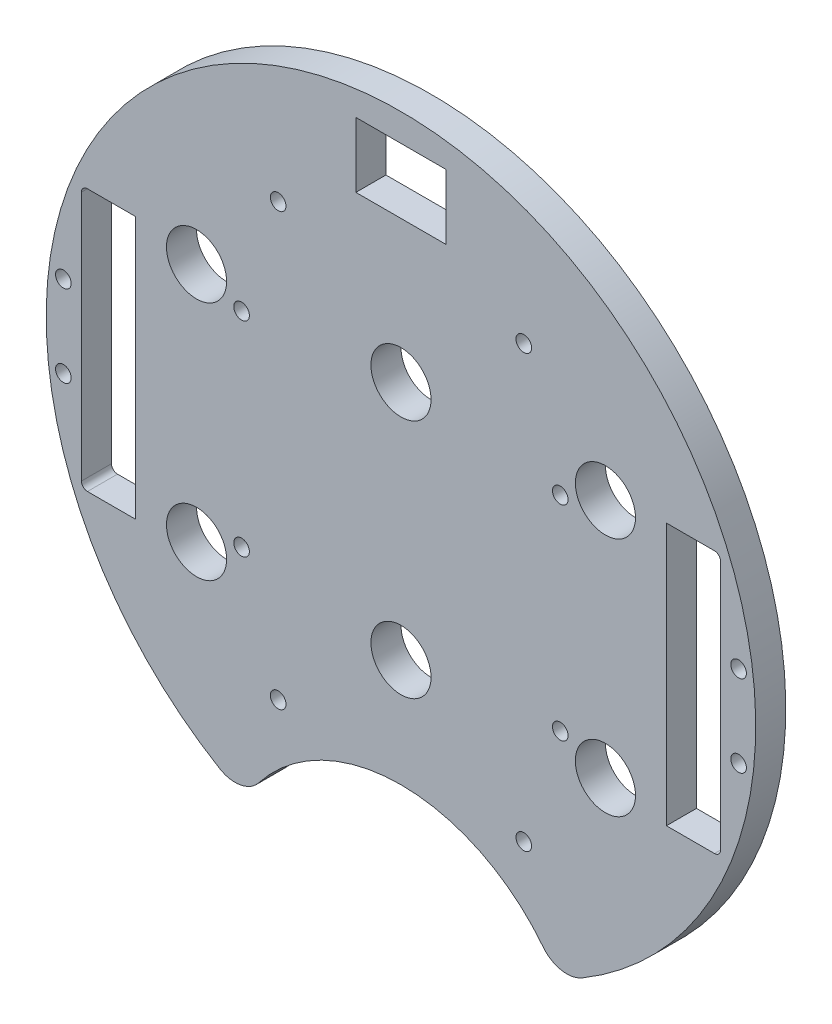
SolidWorks part; units mm, degrees
ref_plane "Front Plane" through (0, 0, 0) normal (0, 0, 1) x (1, 0, 0)
ref_plane "Top Plane" through (0, 0, 0) normal (0, 1, 0) x (1, 0, 0)
ref_plane "Right Plane" through (0, 0, 0) normal (1, 0, 0) x (0, 0, -1)
sketch "Sketch1" plane through (0, 0, 0) normal (0, 0, 1) x (1, 0, 0)
  line L0 (0, 0) -> (-82.1241, 0) construction
  line L1 (0, 0) -> (0, 95.6219) construction
  line L2 (67.494, 26.416) -> (67.494, -26.416)
  line L3 (-66.224, 27.686) -> (-56.064, 27.686)
  line L4 (-67.494, 26.416) -> (-67.494, -26.416)
  line L5 (-66.224, -27.686) -> (-56.064, -27.686)
  line L6 (-56.064, 27.686) -> (-56.064, -27.686)
  line L7 (66.224, -27.686) -> (56.064, -27.686)
  line L8 (66.224, 27.686) -> (56.064, 27.686)
  line L9 (56.064, 27.686) -> (56.064, -27.686)
  arc A0 (-69.526, -27.94) -> (69.526, -27.94) centre (0, 0) ccw
  arc A9 (69.526, 27.94) -> (-69.526, 27.94) centre (0, 0) ccw
  circle A10 centre (0, 0) radius 74.93
  arc A11 (66.224, 27.686) -> (67.494, 26.416) centre (66.224, 26.416) cw
  arc A12 (66.224, -27.686) -> (67.494, -26.416) centre (66.224, -26.416) ccw
  arc A13 (-66.224, 27.686) -> (-67.494, 26.416) centre (-66.224, 26.416) ccw
  arc A14 (-66.224, -27.686) -> (-67.494, -26.416) centre (-66.224, -26.416) cw
  dimension "D13" = 1.27
  dimension "D14" = 1.27
  dimension "D6" = 1.27
  dimension "D7" = 55.372
  dimension "D11" = 27.686
  dimension "D15" = 11.43
extrude "Boss-Extrude2" add sketch "Sketch1" along normal blind 6.35
sketch "Sketch2" plane through (0, 0, 6.35) normal (0, 0, 1) x (1, 0, 0)
  line L1 (-9.525, 69.088) -> (9.525, 69.088)
  line L2 (-9.525, 69.088) -> (-9.525, 55.372)
  line L3 (-9.525, 55.372) -> (9.525, 55.372)
  line L4 (9.525, 69.088) -> (9.525, 55.372)
  circle A3 centre (0, 0) radius 74.93 construction
  dimension "D1" = 19.05
  dimension "D2" = 13.716
  dimension "D3" = 55.372
extrude "Cut-Extrude1" cut sketch "Sketch2" against normal through all
sketch "Sketch3" plane through (0, 0, 6.35) normal (0, 0, 1) x (1, 0, 0)
  line L0 (0, 0) -> (0, -68.8477) construction
  line L1 (-33.02, -67.2621) -> (33.02, -67.2621)
  circle A0 centre (0, 0) radius 74.93 construction
  circle A3 centre (0, -86.3121) radius 38.1
  dimension "D1" = 66.04
  dimension "D2" = 76.2
  dimension "D3" = 0
  dimension "D4" = 19.05
extrude "Cut-Extrude2" cut sketch "Sketch3" against normal through all
extrude "Cut-Extrude3" cut sketch "Sketch4" against normal through all
sketch "Sketch4" plane through (-31.3134, 132.559, 19.05) normal (0, 0, 1) x (0, 1, 0)
  line L0 (-132.559, -31.3134) -> (-245.9178, -31.3134) construction
  line L1 (-132.559, -31.3134) -> (-132.559, -129.4011) construction
  circle A0 centre (-180.819, -4.6434) radius 1.651
  circle A3 centre (-180.819, -57.9834) radius 1.651
  circle A4 centre (-84.299, -57.9834) radius 1.651
  circle A5 centre (-84.299, -4.6434) radius 1.651
extrude "Cut-Extrude4" cut sketch "Sketch5" against normal through all both and the other way through all
sketch "Sketch5" plane through (-31.3134, 132.614, 50.8) normal (0, 0, 1) x (0, 1, 0)
  line L0 (-132.614, -31.3134) -> (-132.614, 57.8454) construction
  line L1 (-132.614, -31.3134) -> (-222.516, -31.3134) construction
  circle A0 centre (-158.014, 14.4066) radius 3.175
  circle A1 centre (-173.254, -31.3134) radius 3.175
  circle A3 centre (-158.014, -77.0334) radius 3.175
  circle A4 centre (-107.214, -77.0334) radius 3.175
  circle A5 centre (-91.974, -31.3134) radius 3.175
  circle A6 centre (-107.214, 14.4066) radius 3.175
fillet "Fillet1" radius 6.35 2 edges at (-33.001, -67.2714, 3.175) (33.001, -67.2714, 3.175)
extrude "Cut-Extrude6" cut sketch "Sketch7" against normal through all and the other way blind 103.378
sketch "Sketch7" plane through (30.092, 4.0835, 6.35) normal (0, 0, -1) x (-1, 0, 0)
  line L0 (30.092, -4.0835) -> (148.6336, -4.0835) construction
  line L1 (30.092, -4.0835) -> (30.092, 90.452) construction
  circle A0 centre (-13.088, 21.3165) radius 3.175
  circle A1 centre (73.272, 21.3165) radius 3.175
  circle A2 centre (30.092, 21.3165) radius 3.175
  circle A4 centre (73.272, -29.4835) radius 3.175
  circle A5 centre (30.092, -29.4835) radius 3.175
  circle A6 centre (-13.088, -29.4835) radius 3.175
extrude "Cut-Extrude7" cut sketch "Sketch8" against normal blind 75.692
sketch "Sketch8" plane through (30.092, 4.0835, -35.052) normal (0, 0, -1) x (-1, 0, 0)
  circle A0 centre (63.7572, 17.5065) radius 1.651
  circle A1 centre (63.7572, -25.6735) radius 1.651
  circle A2 centre (-3.5528, -25.6735) radius 1.651
  circle A3 centre (-3.5528, 17.5065) radius 1.651
extrude "Cut-Extrude9" cut sketch "Sketch10" against normal blind 97.79
sketch "Sketch10" plane through (30.092, 4.0835, -41.275) normal (0, 0, -1) x (-1, 0, 0)
  line L0 (30.092, -29.4835) -> (30.092, 6.2385) construction
  circle A0 centre (4.1544, -49.7288) radius 1.651
  circle A4 centre (56.0296, -49.7288) radius 1.651
  circle A5 centre (4.1544, 41.3825) radius 1.651
  circle A9 centre (56.0296, 41.3825) radius 1.651
extrude "Cut-Extrude10" cut sketch "Sketch11" against normal blind 150.876
sketch "Sketch11" plane through (30.092, 4.0835, 6.35) normal (0, 0, 1) x (1, 0, 0)
  circle A0 centre (-101.396, -12.7195) radius 1.651
  circle A1 centre (-101.396, 4.5525) radius 1.651
  circle A2 centre (41.212, -12.7195) radius 1.651
  circle A3 centre (41.212, 4.5525) radius 1.651
sketch "Sketch12" plane through (0, 0, 6.35) normal (0, 0, 1) x (1, 0, 0)
  circle A0 centre (0, 25.4) radius 6.35
  circle A1 centre (-43.18, 25.4) radius 6.35
  circle A2 centre (-43.18, -25.4) radius 6.35
  circle A3 centre (0, -25.4) radius 6.35
  circle A4 centre (43.18, -25.4) radius 6.35
  circle A5 centre (43.18, 25.4) radius 6.35
  dimension "D1" = 12.7
  dimension "D2" = 12.7
  dimension "D3" = 12.7
  dimension "D4" = 12.7
  dimension "D5" = 12.7
  dimension "D6" = 12.7
extrude "Cut-Extrude11" cut sketch "Sketch12" against normal blind 31.242
